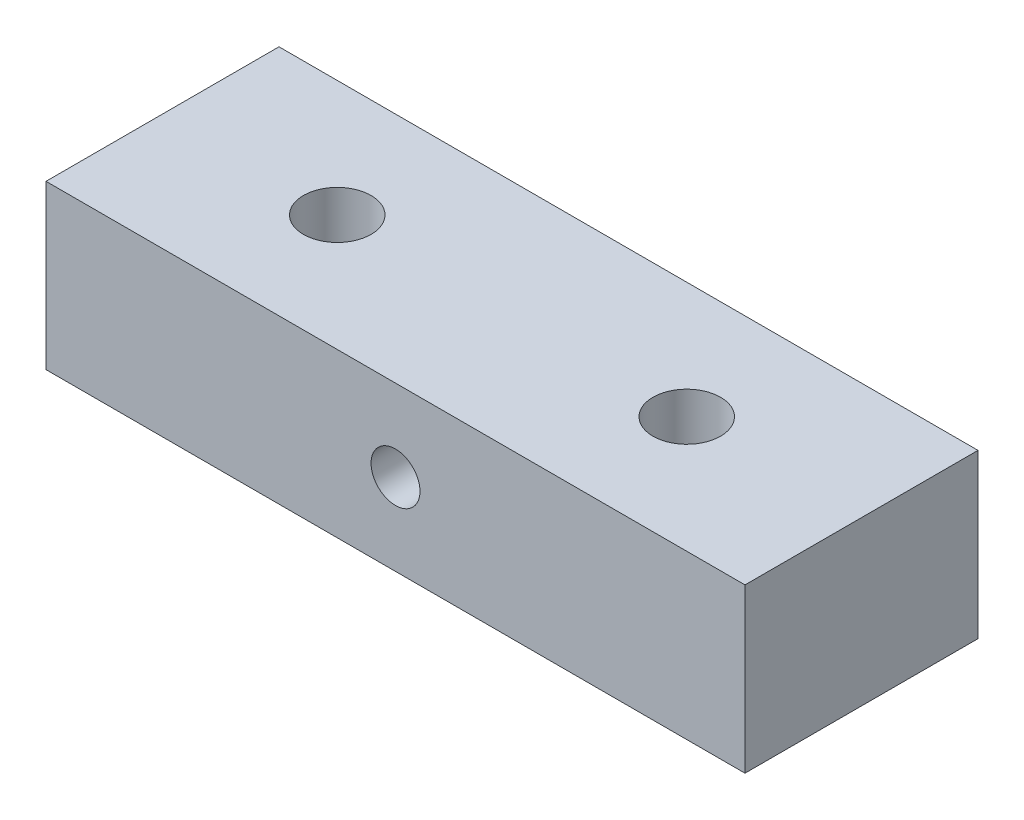
SolidWorks part; units mm, degrees
ref_plane "Front Plane" through (0, 0, 0) normal (0, 0, 1) x (1, 0, 0)
ref_plane "Top Plane" through (0, 0, 0) normal (0, 1, 0) x (1, 0, 0)
ref_plane "Right Plane" through (0, 0, 0) normal (1, 0, 0) x (0, 0, -1)
sketch "Sketch1" plane through (0, 0, 0) normal (0, 0, 1) x (1, 0, 0)
  line L1 (0, 0) -> (30, 0)
  line L2 (0, 0) -> (0, 7)
  line L3 (0, 7) -> (30, 7)
  line L4 (30, 0) -> (30, 7)
  dimension "D1" = 30
  dimension "D2" = 7
extrude "Boss-Extrude1" add sketch "Sketch1" along normal blind 10
sketch "Sketch2" plane through (0, 0, 10) normal (0, 0, 1) x (1, 0, 0)
  line L0 (15, 7) -> (15, 0) construction
  line L1 (30, 7) -> (0, 7) construction
  line L2 (0, 0) -> (30, 0) construction
  circle A0 centre (15, 3.5) radius 1.05
  dimension "D1" = 2.1
extrude "Cut-Extrude1" cut sketch "Sketch2" against normal up to surface (10 mm away) up to face at (15, 3.5, 0)
sketch "Sketch3" plane through (0, 7, 0) normal (0, 1, 0) x (1, 0, 0)
  line L1 (0, -10) -> (0, 0) construction
  line L2 (30, -10) -> (30, 0) construction
  line L3 (30, -5) -> (15, -5) construction
  line L4 (15, -5) -> (0, -5) construction
  line L5 (0, -5) -> (15, -5) construction
  line L6 (15, -5) -> (30, -5) construction
  circle A0 centre (7.5, -5) radius 1.45
  circle A1 centre (22.5, -5) radius 1.45
  dimension "D1" = 2.9
extrude "Cut-Extrude2" cut sketch "Sketch3" against normal through all
